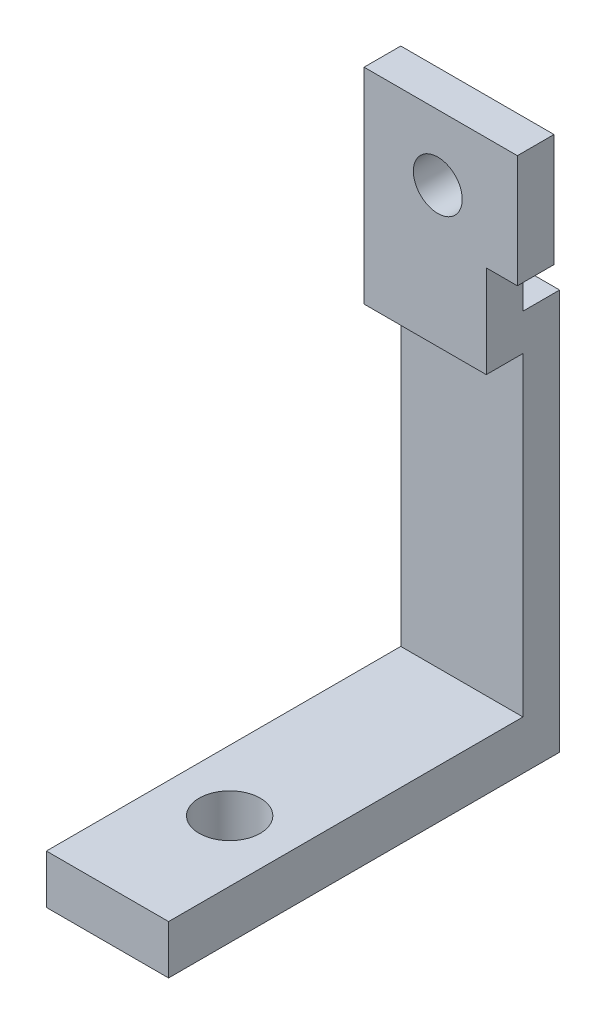
SolidWorks part; units mm, degrees
ref_plane "Front Plane" through (0, 0, 0) normal (0, 0, 1) x (1, 0, 0)
ref_plane "Top Plane" through (0, 0, 0) normal (0, 1, 0) x (1, 0, 0)
ref_plane "Right Plane" through (0, 0, 0) normal (1, 0, 0) x (0, 0, -1)
sketch "Sketch1" plane through (0, 0, 0) normal (0, 1, 0) x (1, 0, 0)
  line L1 (0, 0) -> (10, 0)
  line L2 (0, 0) -> (0, 32)
  line L3 (0, 32) -> (10, 32)
  line L4 (10, 0) -> (10, 32)
extrude "Boss-Extrude1" add sketch "Sketch1" along normal blind 4
sketch "Sketch2" plane through (0, 4, 0) normal (0, 1, 0) x (1, 0, 0)
  circle A0 centre (5, 10) radius 2.5
extrude "Cut-Extrude1" cut sketch "Sketch2" against normal blind 4
sketch "Sketch3" plane through (0, 4, 0) normal (0, 1, 0) x (1, 0, 0)
  line L0 (10, 0) -> (10, 32) construction
  line L1 (0, 32) -> (10, 32)
  line L2 (0, 32) -> (0, 29)
  line L3 (0, 29) -> (10, 29)
  line L4 (10, 32) -> (10, 29)
extrude "Boss-Extrude2" add sketch "Sketch3" along normal blind 28.76
sketch "Sketch4" plane through (0, 0, -29) normal (0, 0, 1) x (1, 0, 0)
  line L1 (0, 32.76) -> (0, 4) construction
  line L2 (10, 46.5524) -> (12.543, 46.5524)
  line L3 (0, 29.76) -> (10, 29.76)
  line L4 (0, 29.76) -> (0, 46.5524)
  line L5 (0, 46.5524) -> (10, 46.5524)
  line L6 (10, 29.76) -> (10, 46.5524)
  line L7 (10, 46.5524) -> (10, 37.3298)
  line L8 (10, 37.3298) -> (12.543, 37.3298)
  line L9 (12.543, 46.5524) -> (12.543, 37.3298)
extrude "Boss-Extrude3" add sketch "Sketch4" along normal blind 3 contours L5 L4 L3 L6 | L7 L8 L9 L2
sketch "Sketch5" plane through (0, 0, -26) normal (0, 0, 1) x (1, 0, 0)
  circle A0 centre (6.0304, 41.1994) radius 2
extrude "Cut-Extrude2" cut sketch "Sketch5" against normal blind 13
